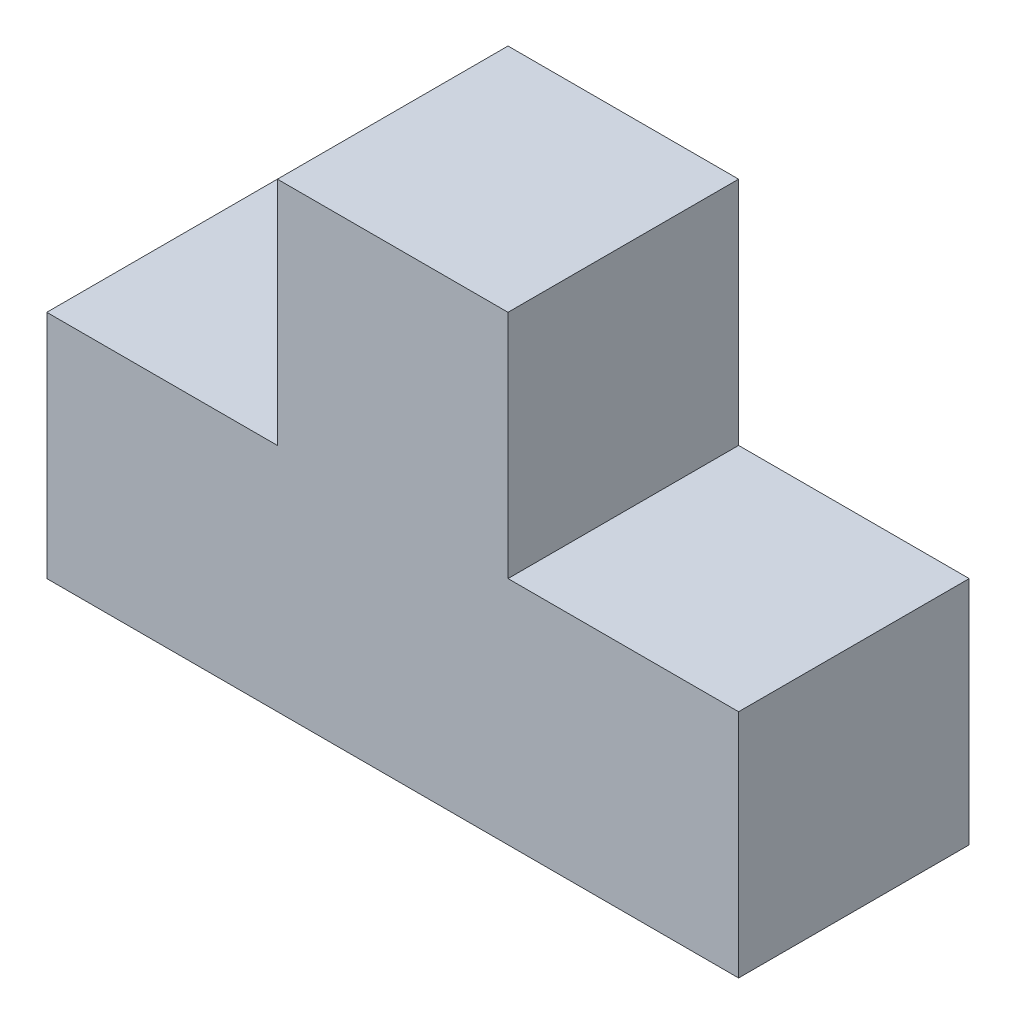
SolidWorks part; units mm, degrees
ref_plane "Plan de face" through (0, 0, 0) normal (0, 0, 1) x (1, 0, 0)
ref_plane "Plan de dessus" through (0, 0, 0) normal (0, 1, 0) x (1, 0, 0)
ref_plane "Plan de droite" through (0, 0, 0) normal (1, 0, 0) x (0, 0, -1)
sketch "Esquisse1" plane through (0, 0, 0) normal (0, 0, 1) x (1, 0, 0)
  line L0 (0, 0) -> (90, 0)
  line L1 (90, 0) -> (90, 30)
  line L2 (90, 30) -> (60, 30)
  line L3 (60, 30) -> (60, 60)
  line L4 (60, 60) -> (30, 60)
  line L5 (30, 60) -> (30, 30)
  line L6 (30, 30) -> (0, 30)
  line L7 (0, 30) -> (0, 0)
  dimension "D1" = 90
  dimension "D2" = 30
  dimension "D3" = 30
  dimension "D4" = 30
  dimension "D5" = 30
  dimension "D6" = 30
extrude "Boss.-Extru.1" add sketch "Esquisse1" along normal blind 30
